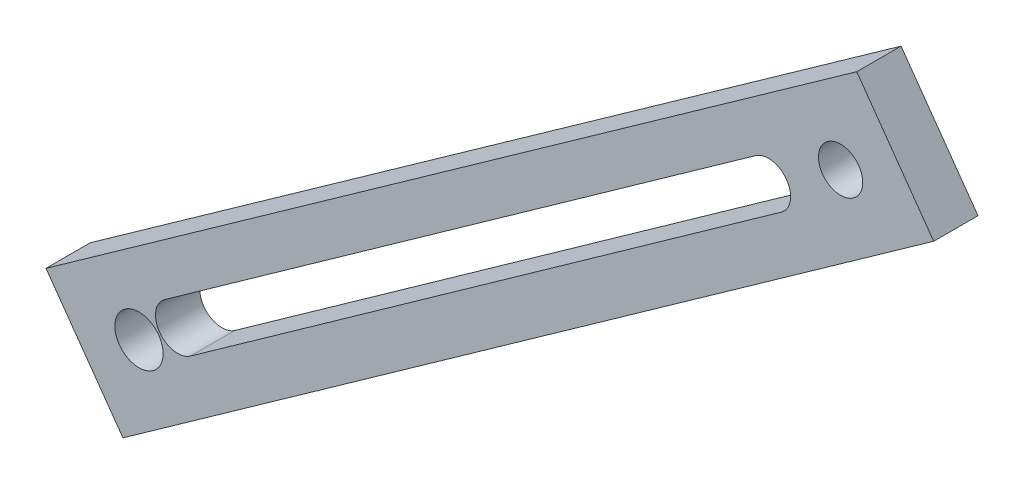
SolidWorks part; units mm, degrees
ref_plane "Front Plane" through (0, 0, 0) normal (0, 0, 1) x (1, 0, 0)
ref_plane "Top Plane" through (0, 0, 0) normal (0, 1, 0) x (1, 0, 0)
ref_plane "Right Plane" through (0, 0, 0) normal (1, 0, 0) x (0, 0, -1)
sketch "Sketch1" plane through (0, 0, 0) normal (0, 0, 1) x (1, 0, 0)
  line L0 (-75.6198, 2.905) -> (-29.1397, 35.9059)
  line L1 (-75.6198, 2.905) -> (-71.2084, -3.3082)
  line L2 (-71.2084, -3.3082) -> (-24.7284, 29.6926)
  line L3 (-24.7284, 29.6926) -> (-29.1397, 35.9059)
  line L4 (-35.1557, 26.8727) -> (-66.2358, 4.7827) construction
  line L5 (-34.4199, 25.8375) -> (-65.5, 3.7475)
  line L6 (-35.8914, 27.9079) -> (-66.9715, 5.8179)
  arc A0 (-34.4199, 25.8375) -> (-35.8914, 27.9079) centre (-35.1557, 26.8727) ccw
  arc A1 (-66.9715, 5.8179) -> (-65.5, 3.7475) centre (-66.2358, 4.7827) ccw
  point P6 (-50.6957, 15.8277)
extrude "Boss-Extrude1" add sketch "Sketch1" along normal blind 2.54 contours L2 L3 L0 L1
sketch "Sketch2" plane through (0, 0, 2.54) normal (0, 0, 1) x (1, 0, 0)
  line L0 (-73.4141, -0.2016) -> (-26.934, 32.7993)
  line L1 (-75.6198, 2.905) -> (-71.2084, -3.3082) construction
  line L2 (-24.7284, 29.6926) -> (-29.1397, 35.9059) construction
  line L3 (-75.6198, 2.905) -> (-72.539, 5.0924)
  line L4 (-75.6198, 2.905) -> (-29.1397, 35.9059) construction
  line L5 (-72.539, 5.0924) -> (-68.1276, -1.1208)
  line L6 (-71.2084, -3.3082) -> (-24.7284, 29.6926) construction
  line L7 (-29.1397, 35.9059) -> (-32.2712, 33.6825)
  line L8 (-32.2712, 33.6825) -> (-27.8598, 27.4693)
  circle A2 centre (-70.2885, 2.0176) radius 1.3848
  circle A3 centre (-30.0655, 30.5759) radius 1.27
extrude "Cut-Extrude2" cut sketch "Sketch2" against normal blind 2.54 contours A3 | A2
sketch "Sketch3" plane through (0, 0, 0) normal (0, 0, -1) x (-1, 0, 0)
  line L0 (68.0736, 3.7241) -> (34.2013, 27.8051) construction
  line L1 (67.3377, 2.689) -> (33.4654, 26.77)
  line L2 (68.8095, 4.7592) -> (34.9372, 28.8402)
  arc A0 (67.3377, 2.689) -> (68.8095, 4.7592) centre (68.0736, 3.7241) ccw
  arc A1 (34.9372, 28.8402) -> (33.4654, 26.77) centre (34.2013, 27.8051) ccw
  point P2 (51.1374, 15.7646)
extrude "Cut-Extrude4" cut sketch "Sketch3" along normal blind 7.62 and the other way blind 10.16 contours L2 A1 L1 A0
